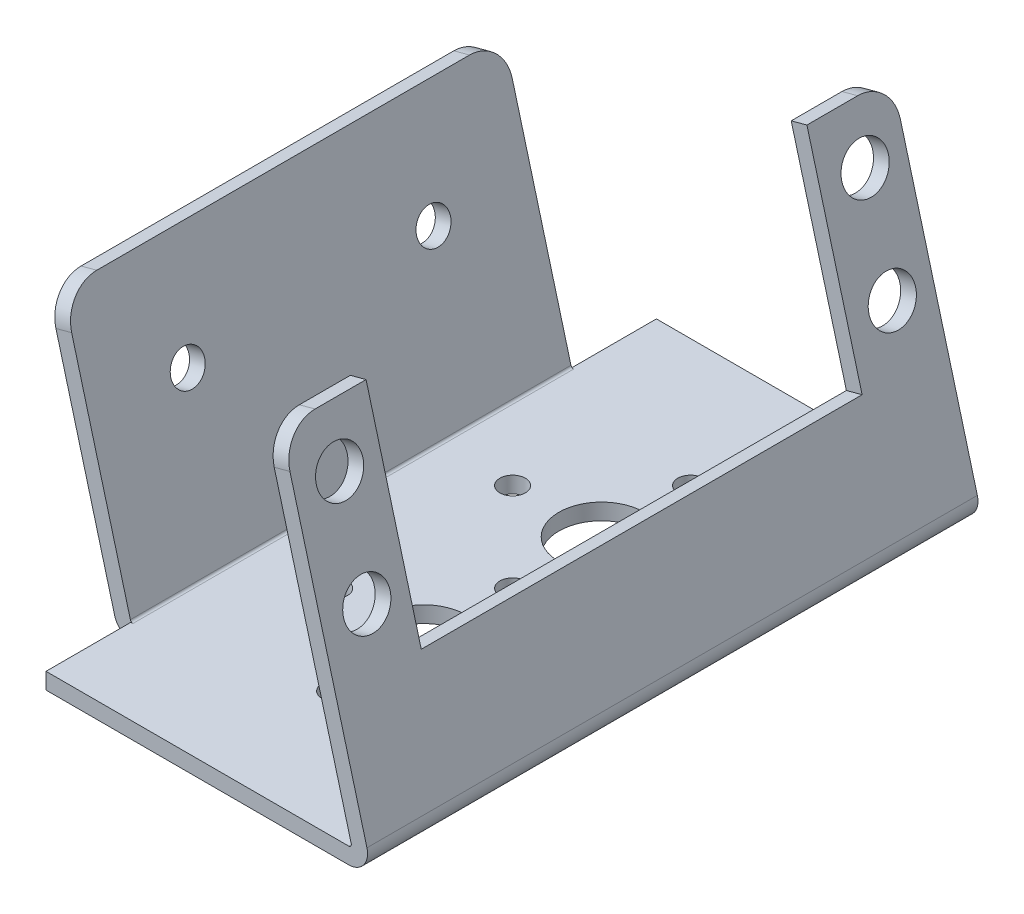
SolidWorks part; units mm, degrees
material "Aluminum"
ref_plane "Front Plane" through (0, 0, 0) normal (0, 0, 1) x (1, 0, 0)
ref_plane "Top Plane" through (0, 0, 0) normal (0, 1, 0) x (1, 0, 0)
ref_plane "Right Plane" through (0, 0, 0) normal (1, 0, 0) x (0, 0, -1)
sketch "Sketch1" plane through (0, 0, 0) normal (0, 0, 1) x (1, 0, 0)
  line L0 (-22.954, 24.9025) -> (-16.2814, 0)
  line L1 (55, 0) -> (-55, 0) construction
  line L2 (-16.2814, 0) -> (15.5368, 0)
  line L3 (15.5368, 0) -> (6.9051, 32.2138)
  line L4 (0, -55) -> (0, 55) construction
  line L5 (-21.4819, 25.297) -> (-15.112, 1.524)
  line L6 (-15.112, 1.524) -> (13.5507, 1.524)
  line L7 (13.5507, 1.524) -> (5.433, 31.8194)
  line L8 (-22.954, 24.9025) -> (-21.4819, 25.297)
  line L9 (5.433, 31.8194) -> (6.9051, 32.2138)
  dimension "D1" = 30.734
  dimension "D2" = 25.781
  dimension "D3" = 33.3502
  dimension "D4" = 16.2814
  dimension "D5" = 105
  dimension "D6" = 1.524
extrude "Extrude1" add sketch "Sketch1" along normal mid plane 57.15
sketch "Sketch2" plane through (0.4326, 0, 10.7304) normal (0, 1, 0) x (-1, 0, 0)
  line L0 (16.714, 17.8446) -> (16.714, -39.3054) construction
  line L1 (0.4326, 5.932) -> (0.4326, -2.3992) construction
  line L2 (16.714, 17.8446) -> (-15.1042, 17.8446) construction
  circle A0 centre (0.4326, -2.3992) radius 4.0005
  circle A1 centre (0.4326, 5.932) radius 1.1938
  circle A2 centre (0.4326, -2.3992) radius 8.3312 construction
  circle A3 centre (8.7638, -2.3992) radius 1.1938
  circle A4 centre (0.4326, -10.7304) radius 1.1938
  circle A5 centre (-7.8986, -2.3992) radius 1.1938
  dimension "D1" = 8.001
  dimension "D2" = 16.6624
  dimension "D3" = 2.3876
  dimension "D4" = 16.2814
  dimension "D5" = 20.2438
extrude "Cut-Extrude1" cut sketch "Sketch2" along normal up to next
sketch "Sketch21" plane through (1.0257, 0, -16.0363) normal (0, 1, 0) x (-1, 0, 0)
  line L0 (17.3071, 44.6113) -> (-14.5111, 44.6113) construction
  line L1 (1.0257, 16.0363) -> (1.0257, 7.7051) construction
  circle A0 centre (1.0257, 7.7051) radius 4.0005
  circle A1 centre (1.0257, 16.0363) radius 1.1938
  circle A2 centre (1.0257, 7.7051) radius 8.3312 construction
  circle A3 centre (9.3569, 7.7051) radius 1.1938
  circle A4 centre (1.0257, -0.6261) radius 1.1938
  circle A5 centre (-7.3055, 7.7051) radius 1.1938
  dimension "D1" = 8.001
  dimension "D2" = 16.6624
  dimension "D3" = 2.3876
  dimension "D4" = 36.9062
extrude "Cut-Extrude11" cut sketch "Sketch21" along normal up to next (1.524 mm away)
sketch "Sketch23" plane through (14.496, 3.8842, 0) normal (0.9659, 0.2588, 0) x (0, 0, -1)
  line L0 (-28.575, 29.329) -> (28.575, 29.329) construction
  line L1 (-20.6248, 29.329) -> (20.6502, 29.329)
  line L2 (-20.6248, 29.329) -> (-20.6248, 9.3646)
  line L3 (-20.6248, 9.3646) -> (20.6502, 9.3646)
  line L4 (20.6502, 29.329) -> (20.6502, 9.3646)
  line L5 (-28.575, -4.0212) -> (-28.575, 29.329) construction
  dimension "D1" = 19.9644
  dimension "D2" = 7.9502
  dimension "D3" = 49.2252
extrude "Cut-Extrude13" cut sketch "Sketch23" against normal up to next
sketch "Sketch24" plane through (14.496, 3.8842, 0) normal (0.9659, 0.2588, 0) x (0, 0, -1)
  line L0 (20.6502, 29.329) -> (28.575, 29.329) construction
  line L1 (-28.575, -4.0212) -> (-28.575, 29.329) construction
  circle A0 centre (-24.4094, 24.2744) radius 2.1844
  circle A1 centre (-24.4094, 14.4446) radius 2.1844
  circle A2 centre (24.7904, 24.2744) radius 2.1844
  circle A3 centre (24.7904, 14.4446) radius 2.1844
  dimension "D1" = 4.3688
  dimension "D2" = 5.0546
  dimension "D4" = 9.8298
  dimension "D6" = 49.1998
  dimension "D3" = 4.1656
  dimension "D5" = 53.3654
extrude "Cut-Extrude14" cut sketch "Sketch24" against normal up to next
sketch "Sketch26" plane through (-15.1908, -4.0703, 0) normal (-0.9659, -0.2588, 0) x (0, 0, 1)
  line L0 (28.575, 29.9949) -> (28.575, 4.2139) construction
  line L1 (28.575, 29.9949) -> (-28.575, 29.9949) construction
  circle A0 centre (-11.5062, 20.0635) radius 1.5875
  circle A1 centre (11.5062, 20.0635) radius 1.5875
  dimension "D1" = 3.175
  dimension "D2" = 17.0688
  dimension "D3" = 40.0812
  dimension "D4" = 9.9314
extrude "Cut-Extrude16" cut sketch "Sketch26" against normal up to next
sketch "Sketch27" plane through (0, 0, 0) normal (0, -1, 0) x (1, 0, 0)
  line L1 (-15.112, 28.575) -> (-27.812, 28.575)
  line L2 (-15.112, 28.575) -> (-15.112, 20.6248)
  line L3 (-15.112, 20.6248) -> (-27.812, 20.6248)
  line L4 (-27.812, 28.575) -> (-27.812, 20.6248)
  line L5 (-15.112, -28.575) -> (-27.812, -28.575)
  line L6 (-15.112, -28.575) -> (-15.112, -20.6248)
  line L7 (-15.112, -20.6248) -> (-27.812, -20.6248)
  line L8 (-27.812, -28.575) -> (-27.812, -20.6248)
  dimension "D1" = 7.9502
  dimension "D2" = 12.7
extrude "Cut-Extrude17" cut sketch "Sketch27" against normal through all
fillet "Fillet1" radius 0.254 2 edges at (13.5507, 1.524, 0) (-15.112, 1.524, 0)
fillet "Fillet2" radius 1.778 2 edges at (15.5368, 0, 0) (-16.2814, 0, 0)
fillet "Fillet3" radius 3.175 4 edges at (6.1691, 32.0166, 28.575) (6.1691, 32.0166, -28.575) (-22.218, 25.0998, -20.6248) (-22.218, 25.0998, 20.6248)
